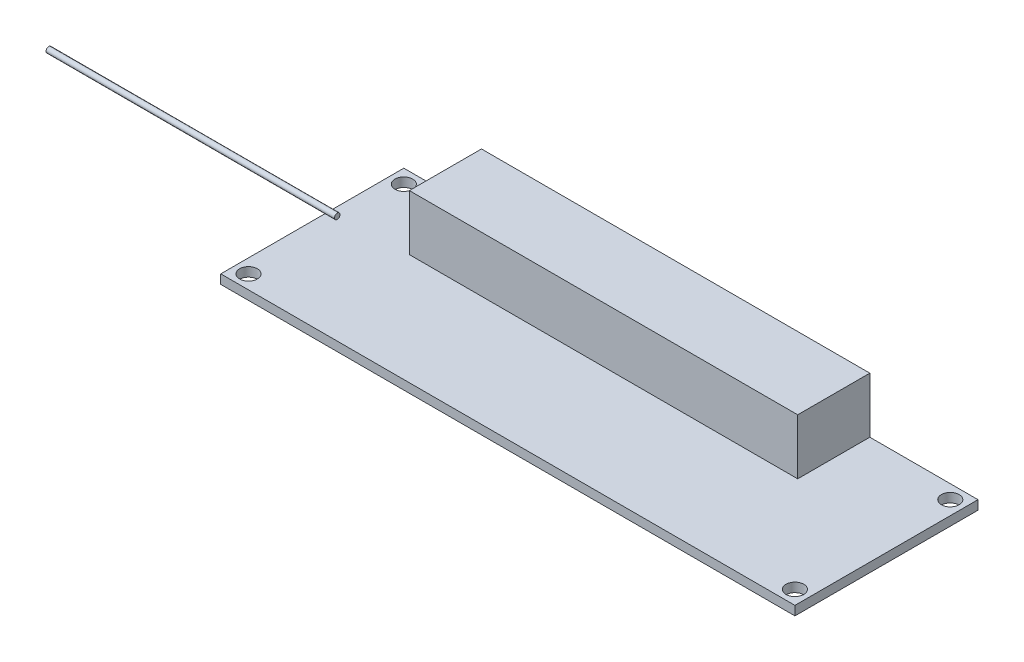
SolidWorks part; units mm, degrees
ref_plane "Ebene vorne" through (0, 0, 0) normal (0, 0, 1) x (1, 0, 0)
ref_plane "Ebene oben" through (0, 0, 0) normal (0, 1, 0) x (1, 0, 0)
ref_plane "Ebene rechts" through (0, 0, 0) normal (1, 0, 0) x (0, 0, -1)
sketch "Skizze1" plane through (0, 0, 0) normal (0, 1, 0) x (1, 0, 0)
  line L1 (-51.75, 16.5) -> (51.75, 16.5)
  line L2 (-51.75, 16.5) -> (-51.75, -16.5)
  line L3 (-51.75, -16.5) -> (51.75, -16.5)
  line L4 (51.75, 16.5) -> (51.75, -16.5)
  dimension "D1" = 103.5
  dimension "D2" = 33
  dimension "D3" = 16.5
  dimension "D4" = 51.75
extrude "Aufsatz-Linear austragen1" add sketch "Skizze1" along normal blind 1.65
sketch "Skizze3" plane through (-51.75, 0, 0) normal (-1, 0, 0) x (0, 0, 1)
  line L0 (-16.5, 1.65) -> (16.5, 1.65) construction
  line L1 (-16.5, 1.65) -> (-16.5, 0) construction
  circle A0 centre (-2.5, 2.15) radius 0.5
  point P4 (-1.8123, 2.15)
  dimension "D2" = 1
  dimension "D1" = 0.5
  dimension "D3" = 14
extrude "Aufsatz-Linear austragen2" add sketch "Skizze3" along normal blind 50 and the other way blind 2 separate body
sketch "Skizze4" plane through (0, 1.65, 0) normal (0, 1, 0) x (1, 0, 0)
  line L0 (51.75, 16.5) -> (-51.75, 16.5) construction
  line L1 (-37.75, 16.5) -> (32.25, 16.5)
  line L2 (-37.75, 16.5) -> (-37.75, 3.5)
  line L3 (-37.75, 3.5) -> (32.25, 3.5)
  line L4 (32.25, 16.5) -> (32.25, 3.5)
  line L5 (-51.75, 16.5) -> (-51.75, -16.5) construction
  dimension "D1" = 70
  dimension "D2" = 0
  dimension "D3" = 14
  dimension "D4" = 13
extrude "Aufsatz-Linear austragen3" add sketch "Skizze4" along normal blind 10
sketch "Skizze6" plane through (0, 1.65, 0) normal (0, 1, 0) x (1, 0, 0)
  line L0 (-51.75, 16.5) -> (-51.75, -16.5) construction
  line L1 (-37.75, 16.5) -> (-51.75, 16.5) construction
  line L2 (0, -0.9075) -> (0, 0.9075) construction
  line L3 (-0.9075, 0) -> (0.9075, 0) construction
  circle A0 centre (-49.25, 14) radius 1.6
  circle A1 centre (49.25, 14) radius 1.6
  circle A2 centre (49.25, -14) radius 1.6
  circle A3 centre (-49.25, -14) radius 1.6
  dimension "D3" = 3.2
  dimension "D1" = 2.5
  dimension "D2" = 2.5
extrude "Schnitt-Linear austragen1" cut sketch "Skizze6" against normal through all
